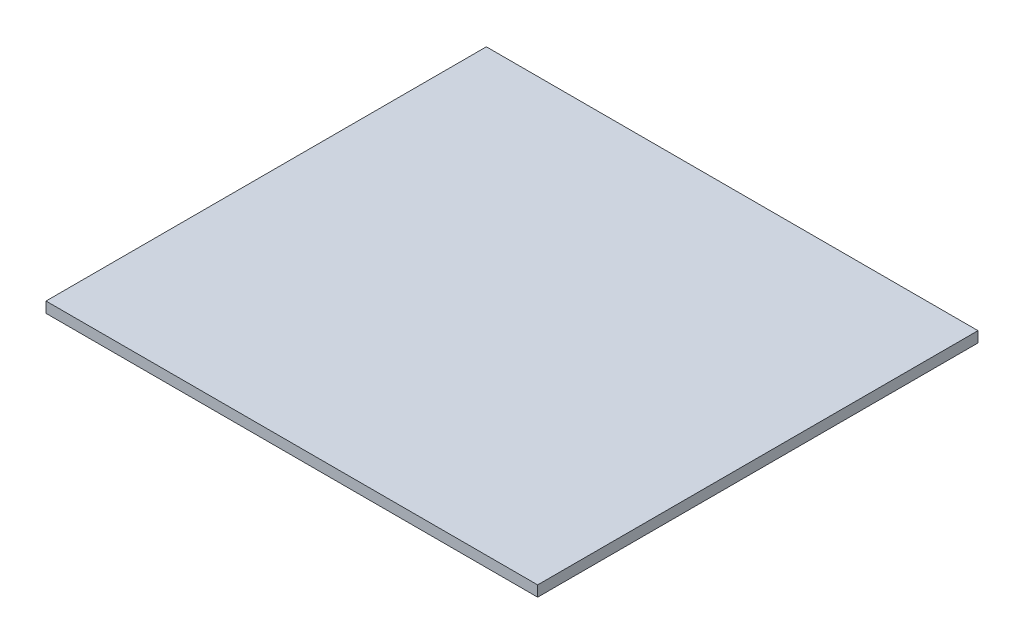
SolidWorks part; units mm, degrees
material "Custom Plastic"
ref_plane "Front Plane" through (0, 0, 0) normal (0, 0, 1) x (1, 0, 0)
ref_plane "Top Plane" through (0, 0, 0) normal (0, 1, 0) x (1, 0, 0)
ref_plane "Right Plane" through (0, 0, 0) normal (1, 0, 0) x (0, 0, -1)
sketch "Sketch1" plane through (0, 0, 0) normal (0, 1, 0) x (1, 0, 0)
  line L1 (-57.5, -51.5) -> (57.5, -51.5)
  line L2 (-57.5, -51.5) -> (-57.5, 51.5)
  line L3 (-57.5, 51.5) -> (57.5, 51.5)
  line L4 (57.5, -51.5) -> (57.5, 51.5)
  line L5 (-57.5, -51.5) -> (57.5, 51.5) construction
  line L6 (-57.5, 51.5) -> (57.5, -51.5) construction
  point P0 (0, 0)
  dimension "D1" = 115
  dimension "D2" = 103
extrude "Boss-Extrude1" add sketch "Sketch1" along normal blind 2.5
ref_plane "Plane1" through (0, 0, 0) normal (0, 0, -1) x (-1, 0, 0)
ref_plane "Plane2" through (0, 0, 0) normal (1, 0, 0) x (0, 0, -1)
ref_plane "Plane3" through (57.5, 2.5, 51.5) normal (0, 0, -1) x (-1, 0, 0)
